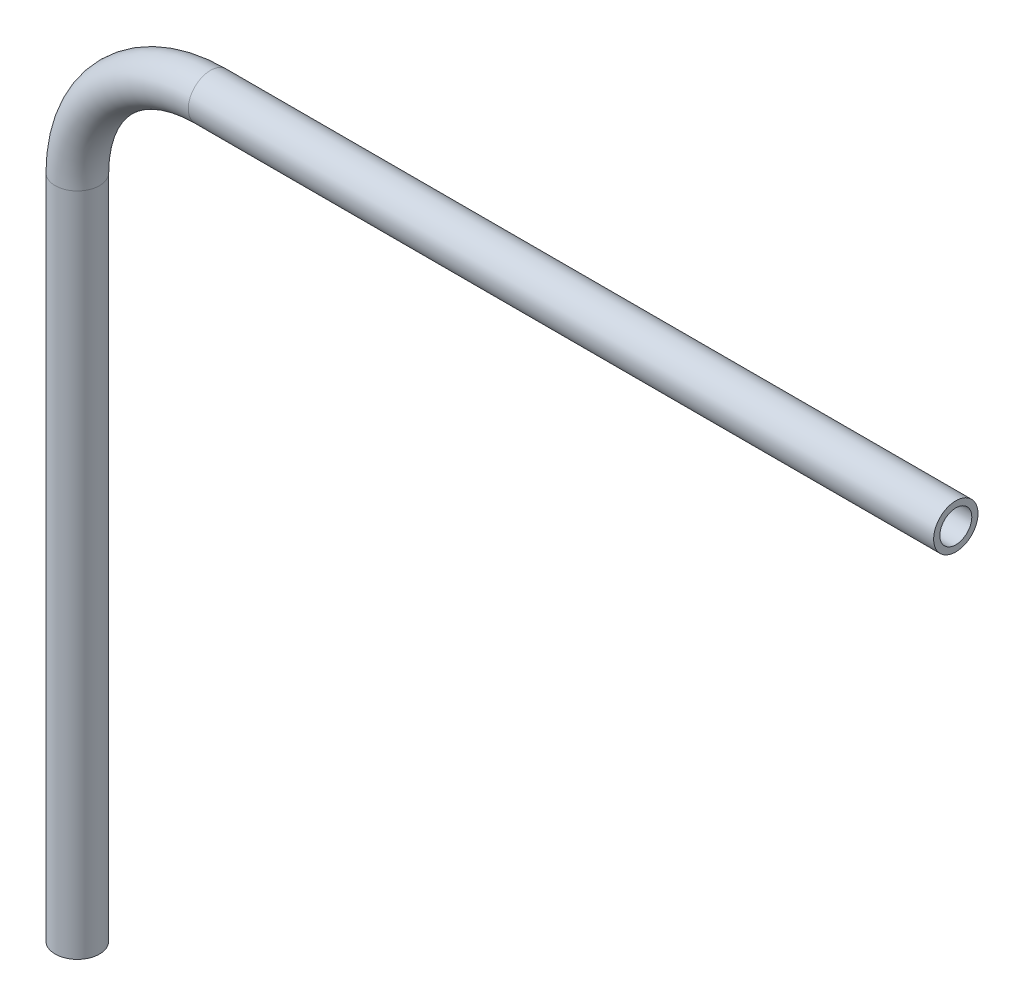
SolidWorks part; units mm, degrees
material "AISI 316 Stainless Steel Sheet (SS)"
ref_plane "Front Plane" through (0, 0, 0) normal (0, 0, 1) x (1, 0, 0)
ref_plane "Top Plane" through (0, 0, 0) normal (0, 1, 0) x (1, 0, 0)
ref_plane "Right Plane" through (0, 0, 0) normal (1, 0, 0) x (0, 0, -1)
sketch "Sketch1" plane through (0, 0, 0) normal (0, 0, 1) x (1, 0, 0)
  line L0 (0, -96.7723) -> (0, -1.5223)
  line L1 (19.05, 17.5277) -> (125.73, 17.5277)
  arc A0 (0, -1.5223) -> (19.05, 17.5277) centre (19.05, -1.5223) cw
  point P6 (0, 17.5277)
  dimension "D3" = 19.05
  dimension "D1" = 125.73
  dimension "D2" = 114.3
ref_plane "Plane1" through (125.73, 17.5277, 0) normal (1, 0, 0) x (0, 0, -1)
sketch "Sketch2" plane through (125.73, 17.5277, 0) normal (1, 0, 0) x (0, 0, -1)
  circle A0 centre (0, 0) radius 3.175
  circle A1 centre (0, 0) radius 2.286
  dimension "D1" = 6.35
  dimension "D2" = 4.572
sweep "Sweep1" add profiles "Sketch2" path "Sketch1"
